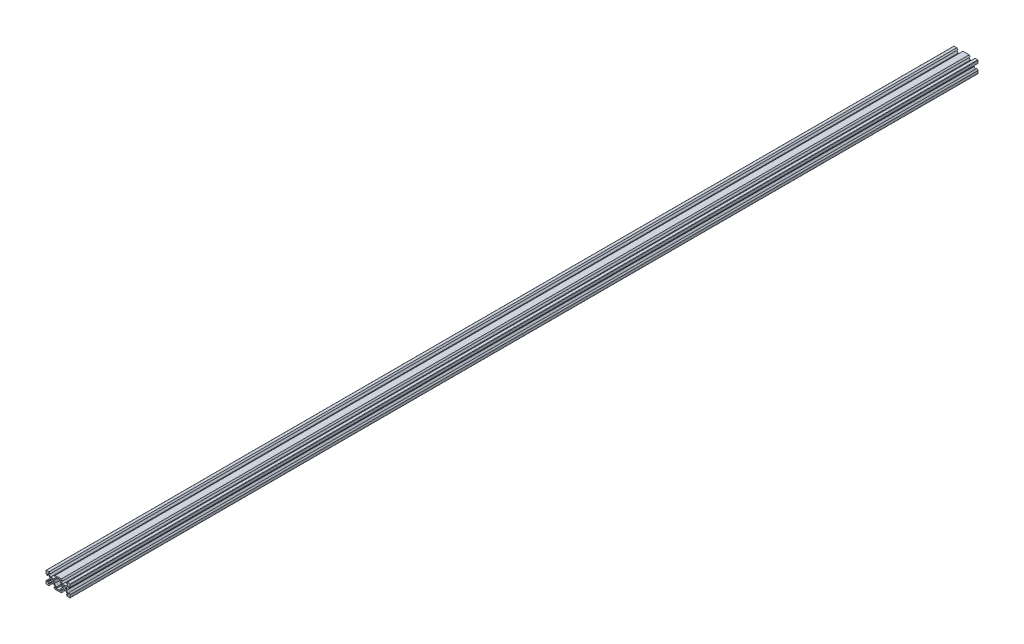
SolidWorks part; units mm, degrees
material "6063-T5"
ref_plane "Front Plane" through (0, 0, 0) normal (0, 0, 1) x (1, 0, 0)
ref_plane "Top Plane" through (0, 0, 0) normal (0, 1, 0) x (1, 0, 0)
ref_plane "Right Plane" through (0, 0, 0) normal (1, 0, 0) x (0, 0, -1)
sketch "Sketch1" plane through (0, 0, 0) normal (0, 0, 1) x (1, 0, 0)
  line L0 (-26.1395, 0) -> (11.0607, 0) construction
  line L1 (0, -20.0817) -> (0, 17.1243) construction
  line L2 (-20, 10.7318) -> (-20, -11.6858) construction
  line L3 (20, 11.8444) -> (20, -11.2237) construction
  line L4 (-23.1467, 10) -> (24.2381, 10) construction
  line L5 (23.8217, -10) -> (-26.7834, -10) construction
  line L6 (3, -5.9393) -> (3, -8)
  line L7 (-20, -10) -> (-15.5, -10)
  line L8 (-20, -10) -> (-20, -5.5)
  line L9 (-18, -5.5) -> (-16.5607, -5.5)
  line L10 (-15.5, -8) -> (-15.5, -6.5607)
  line L11 (-20, 10) -> (-15.5, 10)
  line L12 (-20, 10) -> (-20, 5.5)
  line L13 (-18, 5.5) -> (-16.5607, 5.5)
  line L14 (-15.5, 8) -> (-15.5, 6.5607)
  line L15 (20, 10) -> (15.5, 10)
  line L16 (20, 10) -> (20, 5.5)
  line L17 (18, 5.5) -> (16.5607, 5.5)
  line L18 (15.5, 8) -> (15.5, 6.5607)
  line L19 (20, -10) -> (15.5, -10)
  line L20 (20, -10) -> (20, -5.5)
  line L21 (18, -5.5) -> (16.5607, -5.5)
  line L22 (15.5, -8) -> (15.5, -6.5607)
  line L23 (4.5, -6.5607) -> (4.5, -8)
  line L24 (12.5393, 3.6) -> (15.5, 6.5607)
  line L25 (7.4607, -3.6) -> (4.5, -6.5607)
  line L27 (-4.5, 8) -> (-6.9, 8)
  line L28 (-12.5393, -3.6) -> (-15.5, -6.5607)
  line L29 (7.4607, 3.6) -> (4.5, 6.5607)
  line L30 (12.5393, -3.6) -> (15.5, -6.5607)
  line L31 (-13.6, -2.5393) -> (-16.5607, -5.5)
  line L32 (-13.6, 2.5393) -> (-16.5607, 5.5)
  line L33 (6.4, -2.5393) -> (3, -5.9393)
  line L34 (20, 5.5) -> (20, 5.1)
  line L35 (20, 5.1) -> (18, 3.1)
  line L36 (18, 3.1) -> (18, 5.5)
  line L37 (20, -5.5) -> (20, -5.1)
  line L38 (20, -5.1) -> (18, -3.1)
  line L39 (18, -3.1) -> (18, -5.5)
  line L40 (15.5, 10) -> (15.1, 10)
  line L41 (15.1, 10) -> (13.1, 8)
  line L42 (13.1, 8) -> (15.5, 8)
  line L43 (15.5, -10) -> (15.1, -10)
  line L44 (15.1, -10) -> (13.5138, -8)
  line L45 (13.5138, -8) -> (15.5, -8)
  line L46 (-15.5, 10) -> (-15.1, 10)
  line L47 (-15.1, 10) -> (-13.1, 8)
  line L48 (-13.1, 8) -> (-15.5, 8)
  line L49 (-20, 5.5) -> (-20, 5.1)
  line L50 (-20, 5.1) -> (-18, 3.1)
  line L51 (-18, 3.1) -> (-18, 5.5)
  line L52 (-20, -5.5) -> (-20, -5.1)
  line L53 (-20, -5.1) -> (-18, -3.1)
  line L54 (-18, -3.1) -> (-18, -5.5)
  line L55 (-15.5, -10) -> (-15.1, -10)
  line L56 (-15.1, -10) -> (-13.1, -8)
  line L57 (-13.1, -8) -> (-15.5, -8)
  line L58 (6.4, 2.5393) -> (3, 5.9393)
  line L59 (3, 8) -> (-3, 8)
  line L61 (-3, 5.9393) -> (-3, 8)
  line L62 (-12.5393, 3.6) -> (-15.5, 6.5607)
  line L63 (-4.5, 6.5607) -> (-4.5, 8)
  line L64 (4.5, 6.5607) -> (4.5, 8)
  line L65 (3, 5.9393) -> (3, 8)
  line L66 (13.6, 2.5393) -> (16.5607, 5.5)
  line L67 (12.1, 0) -> (30.0509, 0) construction
  line L68 (-7.4607, 3.6) -> (-4.5, 6.5607)
  line L69 (3, -8) -> (-3, -8)
  line L70 (-6.4, 2.5393) -> (-3, 5.9393)
  line L71 (13.6, -2.5393) -> (16.5607, -5.5)
  line L73 (-3, -5.9393) -> (-3, -8)
  line L74 (-4.5, -6.5607) -> (-4.5, -8)
  line L75 (-7.4607, -3.6) -> (-4.5, -6.5607)
  line L76 (-6.4, -2.5393) -> (-3, -5.9393)
  line L77 (5.3138, -10) -> (7.3138, -8)
  line L78 (7.3138, -8) -> (4.5, -8)
  line L79 (-6.9, -8) -> (-4.9, -10)
  line L80 (-4.9, -10) -> (5.3138, -10)
  line L81 (5.3138, 10) -> (7.3138, 8)
  line L82 (-4.9, 10) -> (5.3138, 10)
  line L83 (-6.9, 8) -> (-4.9, 10)
  line L84 (7.3138, 8) -> (4.5, 8)
  line L85 (7.4607, -3.6) -> (12.5393, -3.6)
  line L86 (-7.4607, -3.6) -> (-12.5393, -3.6)
  line L87 (-6.4, -2.5393) -> (-6.4, 2.5393)
  line L88 (-7.4607, 3.6) -> (-12.5393, 3.6)
  line L89 (-13.6, -2.5393) -> (-13.6, 2.5393)
  line L90 (6.4, -2.5393) -> (6.4, 2.5393)
  line L91 (13.6, -2.5393) -> (13.6, 2.5393)
  line L92 (7.4607, 3.6) -> (12.5393, 3.6)
  line L93 (-4.5, -8) -> (-6.9, -8)
  circle A0 centre (-10, 0) radius 2.1
  circle A1 centre (10, 0) radius 2.1
  dimension "D2" = 4.2
  dimension "D5" = 45
  dimension "D6" = 45
  dimension "D7" = 6.2
  dimension "D8" = 6.2
  dimension "D11" = 3.6
  dimension "D12" = 3.6
  dimension "D38" = 2.4
  dimension "D39" = 45
  dimension "D40" = 2.4
  dimension "D41" = 45
  dimension "D42" = 2
  dimension "D43" = 45
  dimension "D44" = 2.4
  dimension "D45" = 2
  dimension "D49" = 11
extrude "Boss-Extrude1" add sketch "Sketch1" along normal blind 1500
fillet "Fillet1" radius 0.5 4 edges at (-20, -10, 750) (-20, 10, 750) (20, -10, 750) (20, 10, 750)
